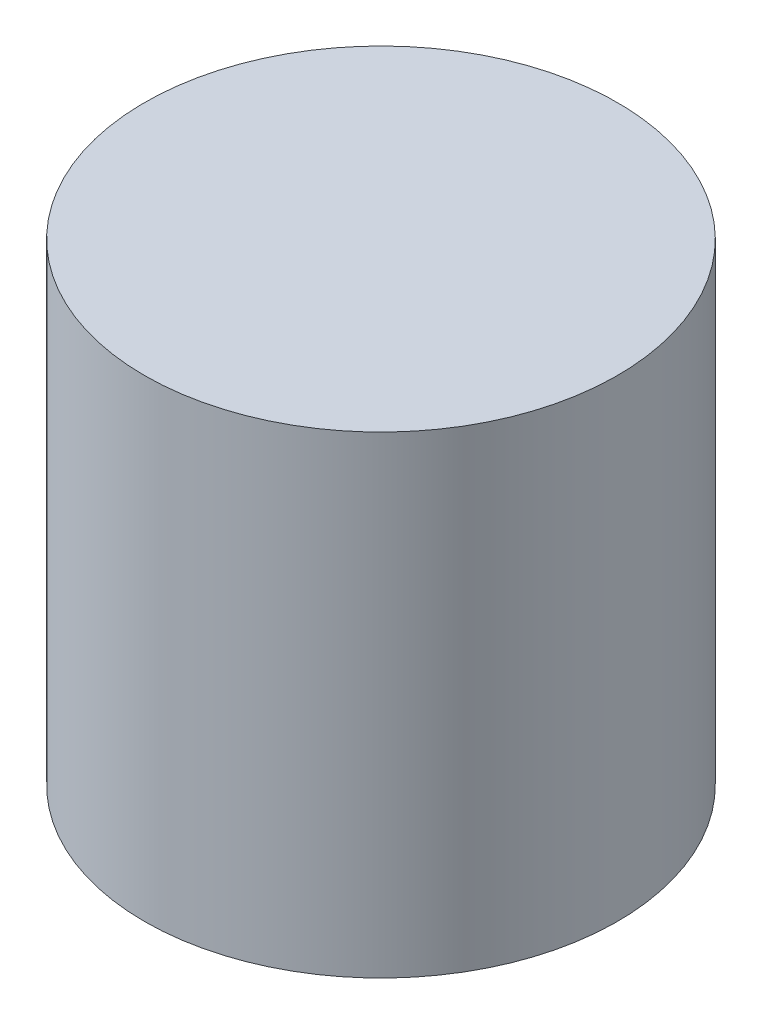
SolidWorks part; units mm, degrees
ref_plane "Front Plane" through (0, 0, 0) normal (0, 0, 1) x (1, 0, 0)
ref_plane "Top Plane" through (0, 0, 0) normal (0, 1, 0) x (1, 0, 0)
ref_plane "Right Plane" through (0, 0, 0) normal (1, 0, 0) x (0, 0, -1)
sketch "Sketch1" plane through (0, 0, 0) normal (0, 1, 0) x (1, 0, 0)
  circle A0 centre (0, 0) radius 5
extrude "Boss-Extrude1" add sketch "Sketch1" along normal blind 10
